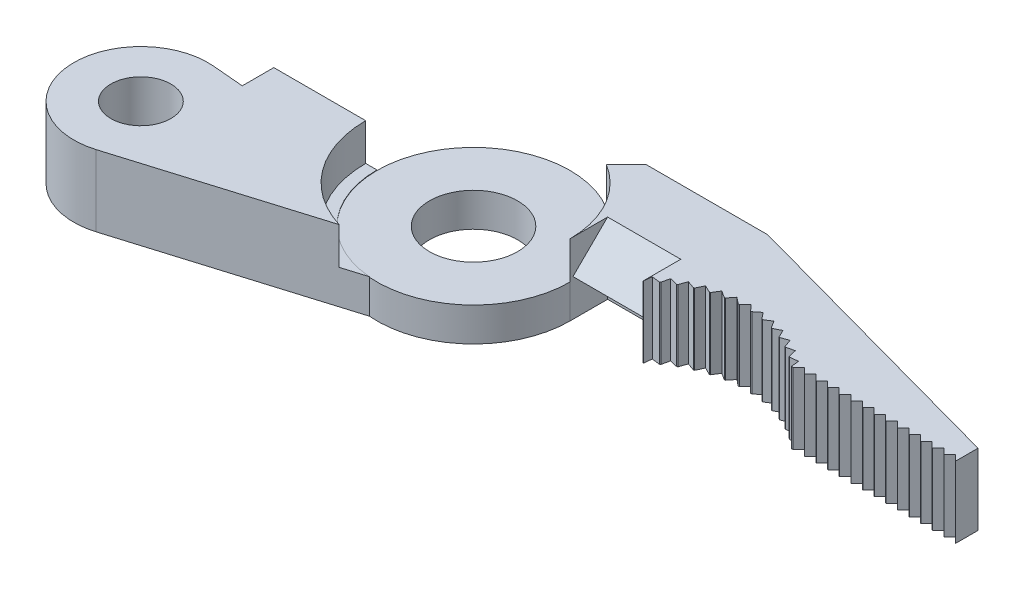
SolidWorks part; units mm, degrees
material "Plain Carbon Steel"
ref_plane "Front Plane" through (0, 0, 0) normal (0, 0, 1) x (1, 0, 0)
ref_plane "Top Plane" through (0, 0, 0) normal (0, 1, 0) x (1, 0, 0)
ref_plane "Right Plane" through (0, 0, 0) normal (1, 0, 0) x (0, 0, -1)
sketch "Sketch1" plane through (0, 0, 0) normal (0, 1, 0) x (1, 0, 0)
  circle A0 centre (0, 0) radius 6.5405
  circle A1 centre (0, 0) radius 2.9845
  dimension "D1" = 13.081
  dimension "D2" = 5.969
extrude "Boss-Extrude1" add sketch "Sketch1" along normal blind 4.826
sketch "Sketch2" plane through (0, 0, 0) normal (0, 1, 0) x (1, 0, 0)
  line L0 (-6.5405, 0) -> (-13.5255, 0)
  line L1 (-13.5255, 0) -> (-13.5255, -2.1377)
  line L2 (-15.6551, -1.9514) -> (-13.5255, -2.1377)
  line L3 (-0.5407, -6.5181) -> (-14.732, -10.8241)
  circle A1 centre (-16.051, -6.477) radius 2.032
  arc A3 (-15.6551, -1.9514) -> (-14.732, -10.8241) centre (-16.051, -6.477) ccw
  arc A4 (-6.5405, 0) -> (-0.5407, -6.5181) centre (0, 0) ccw
  dimension "D1" = 4.064
  dimension "D6" = 6.477
  dimension "D7" = 14.732
  dimension "D3" = 4.5429
  dimension "D4" = 6.5405
  dimension "D2" = 6.985
  dimension "D5" = 85
extrude "Boss-Extrude2" add sketch "Sketch2" along normal up to surface (4.826 mm away) up to face at (0, 4.826, 6.5405)
hole_wizard "#42 (0.0935) Diameter Hole1" positions "Sketch6" profile "Sketch7" hole size "#42" standard "ANSI Inch"
sketch "Sketch6" plane through (0, 0, 0) normal (0, 0, -1) x (-1, 0, 0)
  line L0 (13.5255, 4.826) -> (13.5255, 0) construction
  line L1 (6.5405, 0) -> (13.5255, 0) construction
  point P0 (10.033, 2.413)
  dimension "D1" = 3.4925
  dimension "D2" = 2.413
sketch "Sketch7" plane through (-10.033, 2.413, 0) normal (1, 0, 0) x (0, 1, 0)
  line L0 (0, 0) -> (0, 2.7455)
  line L1 (0, 2.7455) -> (1.1874, 2.032)
  line L2 (1.1874, 2.032) -> (1.1874, 0)
  line L5 (1.1874, 0) -> (0, 0)
  line L10 (0, 2.7455) -> (-1.1875, 2.032) construction
  line L11 (0, -6.35) -> (0, 107.95) construction
  dimension "Hole Dia." = 2.3749
  dimension "Hole Depth" = 2.032
  dimension "Drill Angle" = 118
sketch "Sketch8" plane through (0, 0, 0) normal (0, 1, 0) x (1, 0, 0)
  line L0 (13.0016, 6.9215) -> (32.639, 1.524)
  line L1 (32.639, 1.524) -> (32.639, 0)
  line L2 (32.639, 0) -> (21.5265, 0)
  line L3 (13.0016, 6.9215) -> (4.7466, 6.9215)
  line L4 (4.7466, 6.9215) -> (3.4077, 5.5826)
  line L5 (6.5405, 0) -> (11.4935, 0)
  arc A2 (-0.5407, -6.5181) -> (-6.5405, 0) centre (0, 0) ccw construction
  arc A4 (21.5265, 0) -> (11.4935, 0) centre (16.51, -5.7358) ccw
  arc A5 (6.5405, 0) -> (3.4077, 5.5826) centre (0, 0) ccw
  dimension "D1" = 0.381
  dimension "D8" = 7.62
  dimension "D2" = 1.524
  dimension "D3" = 8.255
  dimension "D4" = 32.639
  dimension "D5" = 225
  dimension "D6" = 11.1125
  dimension "D7" = 16.51
  dimension "D9" = 3.4077
extrude "Boss-Extrude3" add sketch "Sketch8" along normal up to surface (4.826 mm away) up to face at (-10.2571, 4.826, 2.3837)
sketch "Sketch9" plane through (0, 4.826, 0) normal (0, 1, 0) x (1, 0, 0)
  line L2 (-2.1046, -6.9927) -> (-0.5407, -6.5181)
  line L3 (-6.5405, 0) -> (-13.5255, 0) construction
  line L10 (-7.3025, 0) -> (-6.5405, 0)
  line L12 (-14.732, -10.8241) -> (-0.5407, -6.5181) construction
  line L32 (33.401, -0.762) -> (33.401, 2.1048)
  arc A4 (-7.3025, 0) -> (-2.1046, -6.9927) centre (0, 0) ccw
  arc A5 (-6.5405, 0) -> (-0.5407, -6.5181) centre (0, 0) ccw
  arc A6 (3.4077, 5.5826) -> (-6.5405, 0) centre (0, 0) ccw construction
  line M26 (-6.5405, 0) -> (-13.5255, 0)
  line M30 (-14.732, -10.8241) -> (-0.5407, -6.5181)
  dimension "D1" = 7.3025
  dimension "D2" = 6.5405
  dimension "D3" = 33.401
  dimension "D4" = 2.1048
  dimension "D5" = 0.762
extrude "Cut-Extrude1" cut sketch "Sketch9" against normal blind 2.5082 contours A5 A4 M26 M30
sketch "Sketch10" plane through (0, 4.826, 0) normal (0, 1, 0) x (1, 0, 0)
  line L0 (32.639, 0) -> (32.258, 0.381)
  line L1 (32.258, 0.381) -> (31.877, 0)
  line L3 (21.5265, 0) -> (32.639, 0) construction
  line L4 (31.877, 0) -> (32.639, 0)
  dimension "D1" = 0.381
extrude "Cut-Extrude2" cut sketch "Sketch10" against normal through all
pattern_linear "LPattern1" count 14 spacing 0.7874 along (-1, 0, 0) of "Cut-Extrude2"
sketch "Sketch11" plane through (0, 4.826, 0) normal (0, 1, 0) x (1, 0, 0)
  line L0 (21.5265, 0) -> (21.4646, 0.5466)
  line L1 (21.4646, 0.5466) -> (20.9187, 0.4794)
  arc A0 (21.5265, 0) -> (11.4935, 0) centre (16.51, -5.7358) ccw construction
  arc A1 (21.5265, 0) -> (20.9187, 0.4794) centre (16.51, -5.7358) ccw
  dimension "D2" = 4.9546
  dimension "D1" = 8.001
extrude "Cut-Extrude3" cut sketch "Sketch11" against normal through all
pattern_circular "CirPattern1" count 13 over 76.5 about axis through (16.51, 0, 5.7358) along (0, 1, 0) of "Cut-Extrude3"
sketch "Sketch13" plane through (0, 4.826, 0) normal (0, 1, 0) x (1, 0, 0)
  line L0 (11.4935, 0) -> (11.4935, 2.54)
  line L1 (11.4935, 2.54) -> (6.5405, 2.54)
  line L2 (6.5405, 2.54) -> (6.5405, 0)
  line L3 (6.5405, 0) -> (11.4935, 0)
  dimension "D1" = 2.54
extrude "Cut-Extrude5" cut sketch "Sketch13" against normal blind 2.5082
sketch "Sketch14" plane through (6.5405, 0, 0) normal (1, 0, 0) x (0, 0, -1)
  line L0 (0, 2.3178) -> (2.54, 4.826)
  line L1 (2.54, 4.826) -> (2.54, 2.3177)
  line L2 (2.54, 2.3177) -> (2.54, 4.826) construction
  line L3 (2.54, 2.3177) -> (0, 2.3178) construction
  line L4 (2.54, 2.3177) -> (0, 2.3178)
extrude "Boss-Extrude4" add sketch "Sketch14" along normal up to next
sketch "Sketch15" plane through (0, 0, 0) normal (0, -1, 0) x (1, 0, 0)
  line L0 (6.5405, 0) -> (6.5405, -2.54)
  line L1 (6.5405, 0) -> (11.4935, 0) construction
  line L2 (6.5405, -2.54) -> (11.4935, -2.54)
  line L3 (11.4935, -2.54) -> (11.4935, 0)
  line L4 (11.4935, 0) -> (6.5405, 0)
  arc A0 (6.5405, 0) -> (-0.5407, 6.5181) centre (0, 0) ccw construction
  dimension "D1" = 2.54
extrude "Cut-Extrude6" cut sketch "Sketch15" against normal blind 2.5082
sketch "Sketch16" plane through (0, 4.826, 0) normal (0, 1, 0) x (1, 0, 0)
  circle A0 centre (0, 0) radius 6.5405
  dimension "D1" = 13.081
extrude "Cut-Extrude7" cut sketch "Sketch16" against normal blind 2.54
